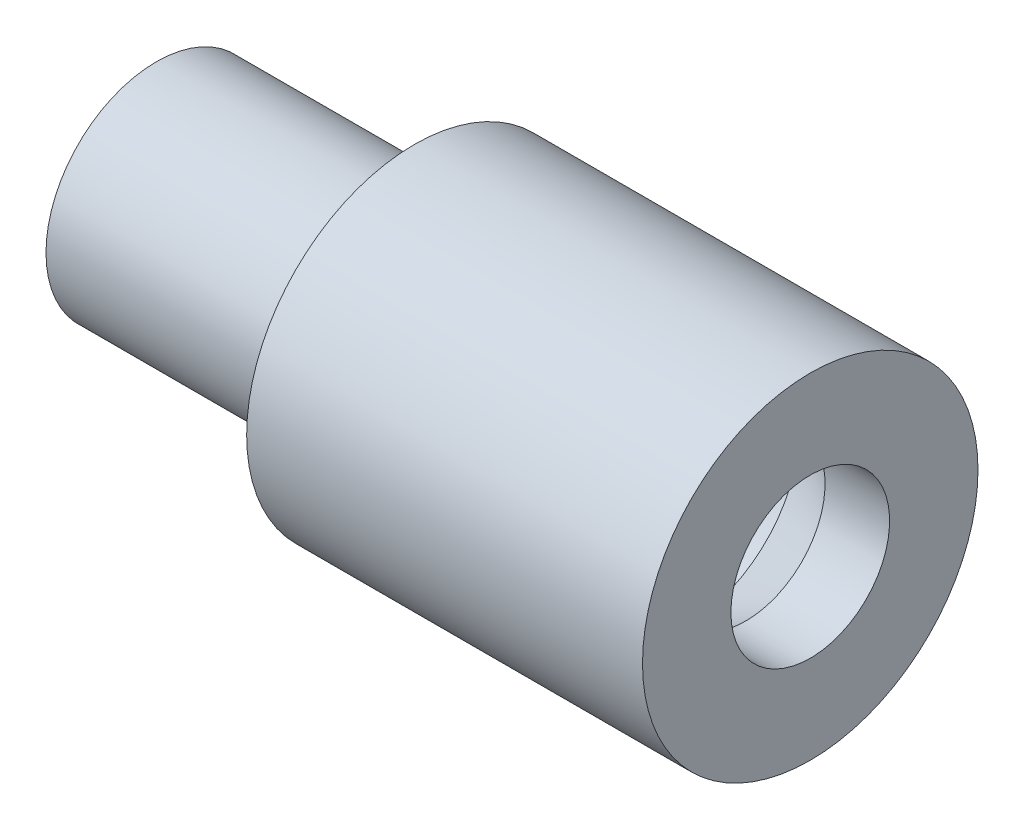
SolidWorks part; units mm, degrees
ref_plane "Front Plane" through (0, 0, 0) normal (0, 0, 1) x (1, 0, 0)
ref_plane "Top Plane" through (0, 0, 0) normal (0, 1, 0) x (1, 0, 0)
ref_plane "Right Plane" through (0, 0, 0) normal (1, 0, 0) x (0, 0, -1)
sketch "Sketch1" plane through (0, 0, 0) normal (0, 1, 0) x (1, 0, 0)
  line L0 (0, 0) -> (0, 21.1838) construction
  line L2 (-5, 4.425) -> (-5, 6.5)
  line L3 (0, 6.5) -> (0, 5.3)
  line L4 (-5, 4.425) -> (-4, 4.425)
  line L6 (0, 5.3) -> (-2, 5.3)
  line L7 (-2, 5.3) -> (-4, 4.425)
  line L8 (0, 5.15) -> (-1.9344, 5.15)
  line L9 (-1.9344, 5.15) -> (-3.9344, 4.275)
  line L10 (-3.9344, 4.275) -> (-5, 4.275)
  line L11 (-5, 4.275) -> (-5, 3.075)
  line L12 (-5, 3.075) -> (0, 3.075)
  line L13 (0, 5.15) -> (0, 3.075)
  line L14 (-5, 4.275) -> (-5, 4.425) construction
  line L15 (-2, 5.3) -> (-2, 5.15) construction
  line L16 (-4, 4.425) -> (-3.9344, 4.275) construction
  line L17 (0, 0) -> (50000, 0) construction
  line L18 (-5, 6.5) -> (0, 6.5)
  point P2 (-2.2605, 5.3)
  dimension "D1" = 13
  dimension "D2" = 6.15
  dimension "D3" = 1.2
  dimension "D4" = 5
  dimension "D5" = 1
  dimension "D6" = 0.15
  dimension "D7" = 1.2
  dimension "D8" = 2.075
  dimension "D9" = 2
  dimension "D10" = 156.371
  dimension "D11" = 4.425
revolve "Revolve1" add sketch "Sketch1" angle 360 about L17
mirror "Mirror1" about plane through (0, 0, 0) normal (1, 0, 0) of "Revolve1"
sketch "Sketch2" plane through (0, 0, 0) normal (0, 1, 0) x (1, 0, 0)
  line L0 (0, 0) -> (50000, 0) construction
  line L1 (5, 4.425) -> (5.5, 4.425)
  line L4 (5, -6.5) -> (5, 6.5) construction
  line L5 (7.8383, 3.075) -> (10.3383, 3.075)
  line L7 (5.5, 4.425) -> (7.8383, 3.075)
  line L8 (10.3383, 3.075) -> (10.3383, 6.5)
  line L9 (10.3383, 6.5) -> (5, 6.5)
  line L10 (5, 6.5) -> (5, 4.425)
  line L11 (5, 6.5) -> (-5, 6.5) construction
  line L12 (5, -4.275) -> (3.9344, -4.275)
  line L13 (3.9344, 4.275) -> (5, 4.275)
  line L14 (4, -4.425) -> (5, -4.425)
  line L15 (5, -4.275) -> (3.9344, -4.275)
  line L16 (5, 4.425) -> (4, 4.425)
  line L17 (5, 4.425) -> (4, 4.425) construction
  line L18 (4, -4.425) -> (5, -4.425)
  point P3 (5, 4.4671)
  point P9 (5, 4.5238)
  point P14 (5, 4.4597)
  point P15 (5, 6.5)
  point P22 (5, 4.3117)
  point P26 (5.5, 4.1517)
  point P27 (5, 4.4067)
  dimension "D1" = 6.15
  dimension "D2" = 0.5
  dimension "D3" = 30
  dimension "D4" = 2.5
revolve "Revolve2" add sketch "Sketch2" angle 360 about L0
sketch "Sketch3" plane through (0, 0, 0) normal (0, 1, 0) x (1, 0, 0)
  line L0 (0, 0) -> (-50000, 0) construction
  line L1 (5, 3.075) -> (-5, 3.075)
  line L2 (-5, -3.075) -> (5, -3.075)
  line L3 (-5, -3.075) -> (5, -3.075)
  line L4 (5, 3.075) -> (-5, 3.075) construction
  line L5 (-5, 4.275) -> (-3.9344, 4.275)
  line L6 (-3.9344, -4.275) -> (-5, -4.275)
  line L7 (-3.9344, -4.275) -> (-5, -4.275)
  line L8 (-5, 4.275) -> (-3.9344, 4.275) construction
  line L9 (-5, 4.275) -> (-15, 4.275)
  line L10 (-15, 4.275) -> (-15, 3.075)
  line L11 (-15, 3.075) -> (-5, 3.075)
  line L12 (-5, 3.075) -> (-5, 4.275)
  dimension "D1" = 10
revolve "Revolve3" add sketch "Sketch3" angle 360 about L0
